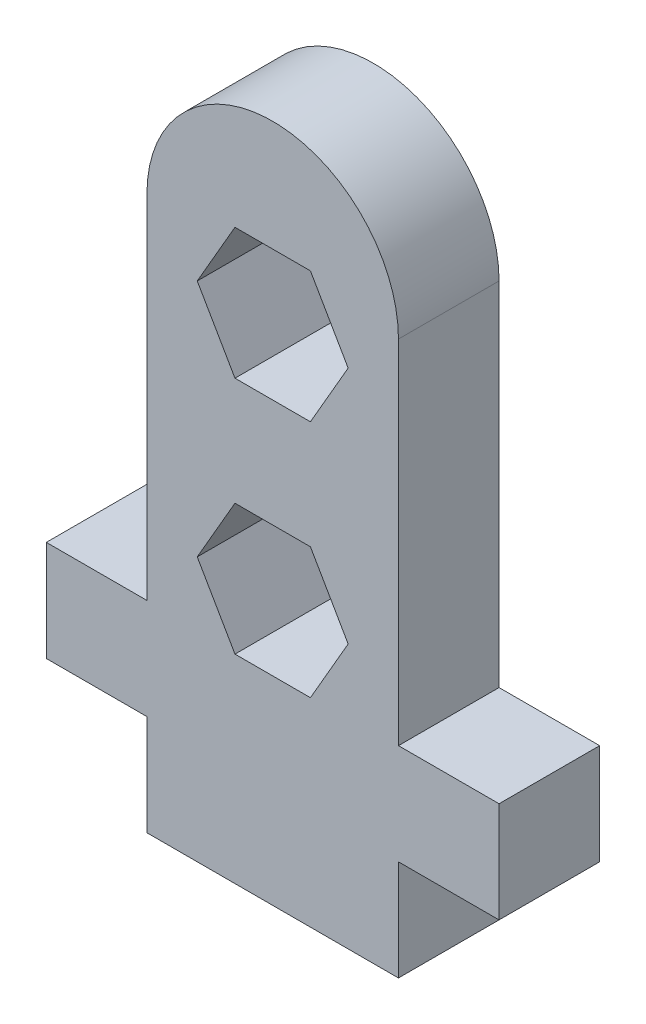
SolidWorks part; units mm, degrees
ref_plane "Front Plane" through (0, 0, 0) normal (0, 0, 1) x (1, 0, 0)
ref_plane "Top Plane" through (0, 0, 0) normal (0, 1, 0) x (1, 0, 0)
ref_plane "Right Plane" through (0, 0, 0) normal (1, 0, 0) x (0, 0, -1)
sketch "Sketch1" plane through (0, 0, 0) normal (0, 0, 1) x (1, 0, 0)
  line L0 (0, 0) -> (10, 0)
  line L1 (0, 0) -> (0, 4)
  line L2 (0, 4) -> (-4, 4)
  line L3 (3.5, 17.4019) -> (6.5, 17.4019)
  line L4 (-4, 4) -> (-4, 8)
  line L5 (-4, 8) -> (0, 8)
  line L6 (0, 8) -> (0, 22)
  line L7 (10, 8) -> (10, 22)
  line L8 (10, 0) -> (10, 4)
  line L9 (14, 8) -> (10, 8)
  line L10 (14, 4) -> (14, 8)
  line L11 (10, 4) -> (14, 4)
  line L12 (3.5, 22.5981) -> (2, 20)
  line L13 (8, 10.5) -> (6.5, 13.0981)
  line L14 (6.5, 13.0981) -> (3.5, 13.0981)
  line L15 (3.5, 13.0981) -> (2, 10.5)
  line L16 (2, 10.5) -> (3.5, 7.9019)
  line L17 (3.5, 7.9019) -> (6.5, 7.9019)
  line L18 (6.5, 7.9019) -> (8, 10.5)
  line L19 (2, 20) -> (3.5, 17.4019)
  line L22 (6.5, 17.4019) -> (8, 20)
  line L23 (8, 20) -> (6.5, 22.5981)
  line L24 (6.5, 22.5981) -> (3.5, 22.5981)
  arc A0 (10, 22) -> (0, 22) centre (5, 22) ccw
  dimension "D5" = 14
  dimension "D6" = 7.9019
  dimension "D1" = 5
  dimension "D2" = 2
  dimension "D3" = 3.5
  dimension "D4" = 6.5
  dimension "D7" = 20
  dimension "D11" = 22
extrude "Boss-Extrude1" add sketch "Sketch1" along normal blind 4
